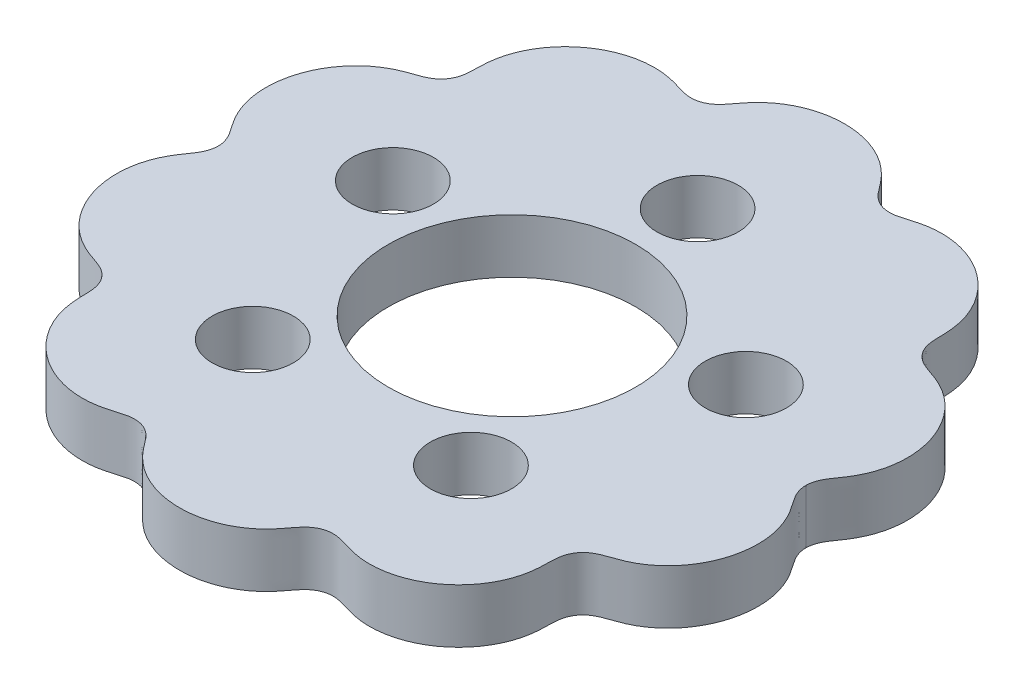
SolidWorks part; units mm, degrees
material "PET"
ref_plane "Front Plane" through (0, 0, 0) normal (0, 0, 1) x (1, 0, 0)
ref_plane "Top Plane" through (0, 0, 0) normal (0, 1, 0) x (1, 0, 0)
ref_plane "Right Plane" through (0, 0, 0) normal (1, 0, 0) x (0, 0, -1)
sketch "Sketch3" plane through (0, 0, 0) normal (0, 1, 0) x (1, 0, 0)
  line L0 (-38, 0) -> (38, 0) construction
  spline S0 degree 4 poles (36.1126, 19.4729) (36.4413, 19.2702) (37.0789, 18.8327) (37.9693, 18.0854) (38.8762, 17.0775) (39.5507, 16.1331) (40.0407, 15.3004) (40.3881, 14.6099) (40.6897, 13.8983) (40.9444, 13.1686) (41.1512, 12.4238) (41.3092, 11.6672) (41.4173, 10.9019) (41.4749, 10.1311) (41.4811, 9.3582) (41.4409, 8.6831) (41.3791, 8.1554) (41.3187, 7.774) (41.2754, 7.5365) (41.2375, 7.3472) (41.1962, 7.1586) (41.1515, 6.9704) (41.1034, 6.7831) (41.0529, 6.5992) (41.0057, 6.4387) (40.9596, 6.292) (40.911, 6.1433) (40.8605, 5.994) (40.8241, 5.8921) (40.7629, 5.7282) (40.696, 5.5563) (40.6301, 5.3943) (40.5534, 5.2164) (40.4594, 5.0098) (40.3608, 4.8047) (40.2582, 4.6024) (40.1246, 4.3522) (39.9561, 4.0563) (39.7484, 3.7177) (39.4981, 3.339) (39.2376, 2.965) (38.9734, 2.5913) (38.7158, 2.2107) (38.4789, 1.8141) (38.1957, 1.2291) (37.9766, 0.4652) (37.9635, -0.3716) (38.1843, -1.2042) (38.4978, -1.8638) (38.846, -2.4146) (39.2404, -2.9665) (39.6428, -3.5471) (40.0239, -4.1584) (40.3719, -4.8049) (40.7581, -5.6601) (41.2492, -7.104) (41.5283, -8.8063) (41.497, -10.7209) (41.0681, -12.9695) (40.261, -15.1202) (39.0103, -17.0606) (37.5039, -18.5357) (36.2533, -19.4084) (35.4358, -19.8689) (34.7726, -20.1839) (34.1039, -20.4514) (33.4364, -20.6827) (32.7933, -20.8983) (32.1897, -21.1442) (31.5529, -21.5019) (30.9312, -22.0245) (30.4594, -22.6931) (30.1741, -23.4534) (30.0458, -24.1722) (30.007, -24.8226) (30.0023, -25.501) (29.9851, -26.2073) (29.932, -26.9257) (29.8311, -27.653) (29.6377, -28.5713) (29.2954, -29.6627) (28.7481, -30.8814) (27.737, -32.4998) (26.4511, -33.9241) (24.9383, -35.11) (22.9085, -36.2017) (21.0718, -36.809) (19.3456, -37.0491) (17.8057, -37.0035) (16.875, -36.8848) (16.1662, -36.7445) (15.49, -36.5679) (14.8442, -36.3701) (14.2164, -36.1743) (13.5933, -36.023) (12.8676, -35.9405) (12.0528, -36.0041) (11.2809, -36.2742) (10.6112, -36.7228) (10.0954, -37.2217) (9.6902, -37.7143) (9.2961, -38.2479) (8.8778, -38.7968) (8.4239, -39.3374) (7.9264, -39.8602) (7.2439, -40.4854) (6.0405, -41.3936) (4.1944, -42.3611) (1.6143, -43.0524) (-1.0601, -43.0726) (-3.3015, -42.6065) (-5.0731, -41.8972) (-6.2345, -41.2367) (-7.1553, -40.5581) (-7.8537, -39.9313) (-8.3647, -39.4039) (-8.8316, -38.8552) (-9.2618, -38.2946) (-9.6641, -37.7484) (-10.0754, -37.2431) (-10.5976, -36.7328) (-11.2728, -36.2773) (-12.0499, -36.0044) (-12.8676, -35.9405) (-13.5933, -36.023) (-14.2164, -36.1743) (-14.8442, -36.3701) (-15.49, -36.5679) (-16.1662, -36.7445) (-16.875, -36.8848) (-17.8057, -37.0035) (-19.3456, -37.0491) (-21.0718, -36.809) (-22.9085, -36.2017) (-24.9383, -35.11) (-26.4511, -33.9241) (-27.737, -32.4998) (-28.7481, -30.8814) (-29.2954, -29.6627) (-29.6377, -28.5713) (-29.8311, -27.653) (-29.932, -26.9257) (-29.9851, -26.2073) (-30.0023, -25.501) (-30.007, -24.8226) (-30.0458, -24.1722) (-30.1741, -23.4534) (-30.4594, -22.6931) (-30.9312, -22.0245) (-31.5529, -21.5019) (-32.1897, -21.1442) (-32.7933, -20.8983) (-33.4364, -20.6827) (-34.1039, -20.4514) (-34.7726, -20.1839) (-35.4358, -19.8689) (-36.2533, -19.4084) (-37.5039, -18.5357) (-39.0102, -17.0606) (-40.4695, -14.7968) (-41.4272, -11.8731) (-41.5902, -9.1846) (-41.2492, -7.104) (-40.758, -5.6601) (-40.3719, -4.8049) (-40.0239, -4.1584) (-39.6428, -3.5471) (-39.2404, -2.9665) (-38.8459, -2.4146) (-38.4978, -1.8639) (-38.1843, -1.2042) (-37.9635, -0.3717) (-37.9784, 0.5829) (-38.2703, 1.4507) (-38.6513, 2.1149) (-38.9734, 2.5914) (-39.2377, 2.965) (-39.4981, 3.339) (-39.7485, 3.7177) (-39.9561, 4.0563) (-40.1246, 4.3522) (-40.2582, 4.6024) (-40.3608, 4.8047) (-40.4594, 5.0098) (-40.5534, 5.2164) (-40.6301, 5.3943) (-40.696, 5.5563) (-40.7629, 5.7282) (-40.8242, 5.8922) (-40.866, 6.0095) (-40.9533, 6.269) (-41.0431, 6.5583) (-41.1159, 6.8262) (-41.1862, 7.1122) (-41.2375, 7.3472) (-41.2754, 7.5365) (-41.3187, 7.774) (-41.3791, 8.1554) (-41.4409, 8.6831) (-41.4811, 9.3582) (-41.4749, 10.1311) (-41.4173, 10.9019) (-41.3092, 11.6672) (-41.1512, 12.4238) (-40.9444, 13.1686) (-40.6897, 13.8983) (-40.3881, 14.6099) (-40.0407, 15.3004) (-39.5507, 16.1331) (-38.8762, 17.0776) (-37.9693, 18.0854) (-37.0789, 18.8327) (-36.4413, 19.2702) (-36.1126, 19.4729) knots 0 0 0 0 0 0.008318 0.016636 0.024955 0.029115 0.033274 0.037433 0.041593 0.045752 0.049911 0.054071 0.05823 0.062389 0.066549 0.070708 0.072787 0.073827 0.074867 0.075907 0.076947 0.077986 0.079026 0.080066 0.081106 0.081626 0.082146 0.083185 0.084407 0.085018 0.085629 0.086851 0.088074 0.089296 0.090518 0.09174 0.092962 0.095406 0.09785 0.100294 0.102738 0.105223 0.107708 0.110193 0.112678 0.119205 0.124677 0.127881 0.131086 0.134889 0.138693 0.142496 0.1463 0.150398 0.154496 0.162692 0.179083 0.187278 0.195474 0.211865 0.228255 0.23645 0.240548 0.244645 0.248449 0.252252 0.256055 0.259858 0.263063 0.266267 0.271739 0.277211 0.280415 0.283619 0.287423 0.291227 0.295031 0.298835 0.302933 0.307031 0.315227 0.323423 0.331619 0.348011 0.35629 0.364568 0.381124 0.389403 0.393542 0.397682 0.401318 0.404955 0.408591 0.412227 0.415486 0.418745 0.424273 0.429682 0.432828 0.435974 0.439689 0.443405 0.44712 0.450835 0.454887 0.458938 0.467041 0.483246 0.499452 0.515845 0.524041 0.532238 0.540434 0.544532 0.548631 0.552435 0.556239 0.560043 0.563848 0.567052 0.570256 0.575727 0.581255 0.584514 0.587773 0.591409 0.595045 0.598682 0.602318 0.606458 0.610597 0.618876 0.635432 0.64371 0.651989 0.668381 0.676577 0.684773 0.692969 0.697067 0.701165 0.704969 0.708773 0.712577 0.716381 0.719585 0.722789 0.728261 0.733733 0.736937 0.740142 0.743945 0.747748 0.751551 0.755355 0.759452 0.76355 0.771745 0.788135 0.804526 0.820917 0.837308 0.845504 0.849602 0.8537 0.857504 0.861307 0.865111 0.868914 0.872119 0.875323 0.880795 0.887322 0.892292 0.894777 0.897262 0.899706 0.90215 0.904594 0.907038 0.90826 0.909482 0.910704 0.911926 0.913149 0.914371 0.914982 0.915593 0.916815 0.917854 0.918894 0.920974 0.923053 0.924093 0.925133 0.926173 0.927213 0.929292 0.933451 0.937611 0.94177 0.945929 0.950089 0.954248 0.958407 0.962567 0.966726 0.970885 0.975045 0.983364 0.991682 1 1 1 1 1 construction
  spline S1 degree 4 poles (38, 0) (38, -0.0025) (38.0002, -0.2591) (38.0411, -0.6644) (38.1843, -1.2042) (38.4978, -1.8638) (38.846, -2.4146) (39.2404, -2.9665) (39.6428, -3.5471) (40.0239, -4.1584) (40.3719, -4.8049) (40.7581, -5.6601) (41.2492, -7.104) (41.5283, -8.8063) (41.497, -10.7209) (41.0681, -12.9695) (40.261, -15.1202) (39.0103, -17.0606) (37.5039, -18.5357) (36.2533, -19.4084) (35.4358, -19.8689) (34.7726, -20.1839) (34.1039, -20.4514) (33.4364, -20.6827) (32.7933, -20.8983) (32.1897, -21.1442) (31.5529, -21.5019) (30.9312, -22.0245) (30.4594, -22.6931) (30.1741, -23.4534) (30.0458, -24.1722) (30.007, -24.8226) (30.0023, -25.501) (29.9851, -26.2073) (29.932, -26.9257) (29.8311, -27.653) (29.6377, -28.5713) (29.2954, -29.6627) (28.7481, -30.8814) (27.737, -32.4998) (26.4511, -33.9241) (24.9383, -35.11) (22.9085, -36.2017) (21.0718, -36.809) (19.3456, -37.0491) (17.8057, -37.0035) (16.875, -36.8848) (16.1662, -36.7445) (15.49, -36.5679) (14.8442, -36.3701) (14.2164, -36.1743) (13.5933, -36.023) (12.8676, -35.9405) (12.0528, -36.0041) (11.2809, -36.2742) (10.6112, -36.7228) (10.0954, -37.2217) (9.6902, -37.7143) (9.2961, -38.2479) (8.8778, -38.7968) (8.4239, -39.3374) (7.9264, -39.8602) (7.2439, -40.4854) (6.0405, -41.3936) (4.1944, -42.3611) (1.6143, -43.0524) (-1.0601, -43.0726) (-3.3015, -42.6065) (-5.0731, -41.8972) (-6.2345, -41.2367) (-7.1553, -40.5581) (-7.8537, -39.9313) (-8.3647, -39.4039) (-8.8316, -38.8552) (-9.2618, -38.2946) (-9.6641, -37.7484) (-10.0754, -37.2431) (-10.5976, -36.7328) (-11.2728, -36.2773) (-12.0499, -36.0044) (-12.8676, -35.9405) (-13.5933, -36.023) (-14.2164, -36.1743) (-14.8442, -36.3701) (-15.49, -36.5679) (-16.1662, -36.7445) (-16.875, -36.8848) (-17.8057, -37.0035) (-19.3456, -37.0491) (-21.0718, -36.809) (-22.9085, -36.2017) (-24.9383, -35.11) (-26.4511, -33.9241) (-27.737, -32.4998) (-28.7481, -30.8814) (-29.2954, -29.6627) (-29.6377, -28.5713) (-29.8311, -27.653) (-29.932, -26.9257) (-29.9851, -26.2073) (-30.0023, -25.501) (-30.007, -24.8226) (-30.0458, -24.1722) (-30.1741, -23.4534) (-30.4594, -22.6931) (-30.9312, -22.0245) (-31.5529, -21.5019) (-32.1897, -21.1442) (-32.7933, -20.8983) (-33.4364, -20.6827) (-34.1039, -20.4514) (-34.7726, -20.1839) (-35.4358, -19.8689) (-36.2533, -19.4084) (-37.5039, -18.5357) (-39.0102, -17.0606) (-40.4695, -14.7968) (-41.4272, -11.8731) (-41.5902, -9.1846) (-41.2492, -7.104) (-40.758, -5.6601) (-40.3719, -4.8049) (-40.0239, -4.1584) (-39.6428, -3.5471) (-39.2404, -2.9665) (-38.8459, -2.4146) (-38.4978, -1.8639) (-38.1843, -1.2042) (-38.0411, -0.6644) (-38.0002, -0.2591) (-38, -0.0025) (-38, 0) knots 0.119151 0.119151 0.119151 0.119151 0.119151 0.119205 0.124677 0.127881 0.131086 0.134889 0.138693 0.142496 0.1463 0.150398 0.154496 0.162692 0.179083 0.187278 0.195474 0.211865 0.228255 0.23645 0.240548 0.244645 0.248449 0.252252 0.256055 0.259858 0.263063 0.266267 0.271739 0.277211 0.280415 0.283619 0.287423 0.291227 0.295031 0.298835 0.302933 0.307031 0.315227 0.323423 0.331619 0.348011 0.35629 0.364568 0.381124 0.389403 0.393542 0.397682 0.401318 0.404955 0.408591 0.412227 0.415486 0.418745 0.424273 0.429682 0.432828 0.435974 0.439689 0.443405 0.44712 0.450835 0.454887 0.458938 0.467041 0.483246 0.499452 0.515845 0.524041 0.532238 0.540434 0.544532 0.548631 0.552435 0.556239 0.560043 0.563848 0.567052 0.570256 0.575727 0.581255 0.584514 0.587773 0.591409 0.595045 0.598682 0.602318 0.606458 0.610597 0.618876 0.635432 0.64371 0.651989 0.668381 0.676577 0.684773 0.692969 0.697067 0.701165 0.704969 0.708773 0.712577 0.716381 0.719585 0.722789 0.728261 0.733733 0.736937 0.740142 0.743945 0.747748 0.751551 0.755355 0.759452 0.76355 0.771745 0.788135 0.804526 0.820917 0.837308 0.845504 0.849602 0.8537 0.857504 0.861307 0.865111 0.868914 0.872119 0.875323 0.880795 0.880849 0.880849 0.880849 0.880849 0.880849
  spline S2 degree 4 poles (38, 0) (38, 0.0025) (38.0002, 0.2591) (38.0411, 0.6644) (38.1843, 1.2042) (38.4978, 1.8638) (38.846, 2.4146) (39.2404, 2.9665) (39.6428, 3.5471) (40.0239, 4.1584) (40.3719, 4.8049) (40.7581, 5.6601) (41.2492, 7.104) (41.5283, 8.8063) (41.497, 10.7209) (41.0681, 12.9695) (40.261, 15.1202) (39.0103, 17.0606) (37.5039, 18.5357) (36.2533, 19.4084) (35.4358, 19.8689) (34.7726, 20.1839) (34.1039, 20.4514) (33.4364, 20.6827) (32.7933, 20.8983) (32.1897, 21.1442) (31.5529, 21.5019) (30.9312, 22.0245) (30.4594, 22.6931) (30.1741, 23.4534) (30.0458, 24.1722) (30.007, 24.8226) (30.0023, 25.501) (29.9851, 26.2073) (29.932, 26.9257) (29.8311, 27.653) (29.6377, 28.5713) (29.2954, 29.6627) (28.7481, 30.8814) (27.737, 32.4998) (26.4511, 33.9241) (24.9383, 35.11) (22.9085, 36.2017) (21.0718, 36.809) (19.3456, 37.0491) (17.8057, 37.0035) (16.875, 36.8848) (16.1662, 36.7445) (15.49, 36.5679) (14.8442, 36.3701) (14.2164, 36.1743) (13.5933, 36.023) (12.8676, 35.9405) (12.0528, 36.0041) (11.2809, 36.2742) (10.6112, 36.7228) (10.0954, 37.2217) (9.6902, 37.7143) (9.2961, 38.2479) (8.8778, 38.7968) (8.4239, 39.3374) (7.9264, 39.8602) (7.2439, 40.4854) (6.0405, 41.3936) (4.1944, 42.3611) (1.6143, 43.0524) (-1.0601, 43.0726) (-3.3015, 42.6065) (-5.0731, 41.8972) (-6.2345, 41.2367) (-7.1553, 40.5581) (-7.8537, 39.9313) (-8.3647, 39.4039) (-8.8316, 38.8552) (-9.2618, 38.2946) (-9.6641, 37.7484) (-10.0754, 37.2431) (-10.5976, 36.7328) (-11.2728, 36.2773) (-12.0499, 36.0044) (-12.8676, 35.9405) (-13.5933, 36.023) (-14.2164, 36.1743) (-14.8442, 36.3701) (-15.49, 36.5679) (-16.1662, 36.7445) (-16.875, 36.8848) (-17.8057, 37.0035) (-19.3456, 37.0491) (-21.0718, 36.809) (-22.9085, 36.2017) (-24.9383, 35.11) (-26.4511, 33.9241) (-27.737, 32.4998) (-28.7481, 30.8814) (-29.2954, 29.6627) (-29.6377, 28.5713) (-29.8311, 27.653) (-29.932, 26.9257) (-29.9851, 26.2073) (-30.0023, 25.501) (-30.007, 24.8226) (-30.0458, 24.1722) (-30.1741, 23.4534) (-30.4594, 22.6931) (-30.9312, 22.0245) (-31.5529, 21.5019) (-32.1897, 21.1442) (-32.7933, 20.8983) (-33.4364, 20.6827) (-34.1039, 20.4514) (-34.7726, 20.1839) (-35.4358, 19.8689) (-36.2533, 19.4084) (-37.5039, 18.5357) (-39.0102, 17.0606) (-40.4695, 14.7968) (-41.4272, 11.8731) (-41.5902, 9.1846) (-41.2492, 7.104) (-40.758, 5.6601) (-40.3719, 4.8049) (-40.0239, 4.1584) (-39.6428, 3.5471) (-39.2404, 2.9665) (-38.8459, 2.4146) (-38.4978, 1.8639) (-38.1843, 1.2042) (-38.0411, 0.6644) (-38.0002, 0.2591) (-38, 0.0025) (-38, 0) knots 0.119151 0.119151 0.119151 0.119151 0.119151 0.119205 0.124677 0.127881 0.131086 0.134889 0.138693 0.142496 0.1463 0.150398 0.154496 0.162692 0.179083 0.187278 0.195474 0.211865 0.228255 0.23645 0.240548 0.244645 0.248449 0.252252 0.256055 0.259858 0.263063 0.266267 0.271739 0.277211 0.280415 0.283619 0.287423 0.291227 0.295031 0.298835 0.302933 0.307031 0.315227 0.323423 0.331619 0.348011 0.35629 0.364568 0.381124 0.389403 0.393542 0.397682 0.401318 0.404955 0.408591 0.412227 0.415486 0.418745 0.424273 0.429682 0.432828 0.435974 0.439689 0.443405 0.44712 0.450835 0.454887 0.458938 0.467041 0.483246 0.499452 0.515845 0.524041 0.532238 0.540434 0.544532 0.548631 0.552435 0.556239 0.560043 0.563848 0.567052 0.570256 0.575727 0.581255 0.584514 0.587773 0.591409 0.595045 0.598682 0.602318 0.606458 0.610597 0.618876 0.635432 0.64371 0.651989 0.668381 0.676577 0.684773 0.692969 0.697067 0.701165 0.704969 0.708773 0.712577 0.716381 0.719585 0.722789 0.728261 0.733733 0.736937 0.740142 0.743945 0.747748 0.751551 0.755355 0.759452 0.76355 0.771745 0.788135 0.804526 0.820917 0.837308 0.845504 0.849602 0.8537 0.857504 0.861307 0.865111 0.868914 0.872119 0.875323 0.880795 0.880849 0.880849 0.880849 0.880849 0.880849
extrude "Boss-Extrude2" add sketch "Sketch3" along normal blind 7
sketch "Sketch4" plane through (0, 7, 0) normal (0, 1, 0) x (1, 0, 0)
  line L0 (0, 0) -> (40.8955, 13.2876) construction
  circle A0 centre (0, 0) radius 16
  circle A1 centre (22.8254, 7.4164) radius 5.25
  circle A2 centre (14.1068, -19.4164) radius 5.25
  circle A3 centre (-14.1069, -19.4164) radius 5.25
  circle A4 centre (-22.8253, 7.4165) radius 5.25
  circle A5 centre (0.0001, 24) radius 5.25
  spline S0 degree 4 poles (38, 0) (38, 0.0025) (38.0002, 0.2591) (38.0411, 0.6644) (38.1843, 1.2042) (38.4978, 1.8638) (38.846, 2.4146) (39.2404, 2.9665) (39.6428, 3.5471) (40.0239, 4.1584) (40.3719, 4.8049) (40.7581, 5.6601) (41.2492, 7.104) (41.5283, 8.8063) (41.497, 10.7209) (41.0681, 12.9695) (40.261, 15.1202) (39.0103, 17.0606) (37.5039, 18.5357) (36.2533, 19.4084) (35.4358, 19.8689) (34.7726, 20.1839) (34.1039, 20.4514) (33.4364, 20.6827) (32.7933, 20.8983) (32.1897, 21.1442) (31.5529, 21.5019) (30.9312, 22.0245) (30.4594, 22.6931) (30.1741, 23.4534) (30.0458, 24.1722) (30.007, 24.8226) (30.0023, 25.501) (29.9851, 26.2073) (29.932, 26.9257) (29.8311, 27.653) (29.6377, 28.5713) (29.2954, 29.6627) (28.7481, 30.8814) (27.737, 32.4998) (26.4511, 33.9241) (24.9383, 35.11) (22.9085, 36.2017) (21.0718, 36.809) (19.3456, 37.0491) (17.8057, 37.0035) (16.875, 36.8848) (16.1662, 36.7445) (15.49, 36.5679) (14.8442, 36.3701) (14.2164, 36.1743) (13.5933, 36.023) (12.8676, 35.9405) (12.0528, 36.0041) (11.2809, 36.2742) (10.6112, 36.7228) (10.0954, 37.2217) (9.6902, 37.7143) (9.2961, 38.2479) (8.8778, 38.7968) (8.4239, 39.3374) (7.9264, 39.8602) (7.2439, 40.4854) (6.0405, 41.3936) (4.1944, 42.3611) (1.6143, 43.0524) (-1.0601, 43.0726) (-3.3015, 42.6065) (-5.0731, 41.8972) (-6.2345, 41.2367) (-7.1553, 40.5581) (-7.8537, 39.9313) (-8.3647, 39.4039) (-8.8316, 38.8552) (-9.2618, 38.2946) (-9.6641, 37.7484) (-10.0754, 37.2431) (-10.5976, 36.7328) (-11.2728, 36.2773) (-12.0499, 36.0044) (-12.8676, 35.9405) (-13.5933, 36.023) (-14.2164, 36.1743) (-14.8442, 36.3701) (-15.49, 36.5679) (-16.1662, 36.7445) (-16.875, 36.8848) (-17.8057, 37.0035) (-19.3456, 37.0491) (-21.0718, 36.809) (-22.9085, 36.2017) (-24.9383, 35.11) (-26.4511, 33.9241) (-27.737, 32.4998) (-28.7481, 30.8814) (-29.2954, 29.6627) (-29.6377, 28.5713) (-29.8311, 27.653) (-29.932, 26.9257) (-29.9851, 26.2073) (-30.0023, 25.501) (-30.007, 24.8226) (-30.0458, 24.1722) (-30.1741, 23.4534) (-30.4594, 22.6931) (-30.9312, 22.0245) (-31.5529, 21.5019) (-32.1897, 21.1442) (-32.7933, 20.8983) (-33.4364, 20.6827) (-34.1039, 20.4514) (-34.7726, 20.1839) (-35.4358, 19.8689) (-36.2533, 19.4084) (-37.5039, 18.5357) (-39.0102, 17.0606) (-40.4695, 14.7968) (-41.4272, 11.8731) (-41.5902, 9.1846) (-41.2492, 7.104) (-40.758, 5.6601) (-40.3719, 4.8049) (-40.0239, 4.1584) (-39.6428, 3.5471) (-39.2404, 2.9665) (-38.8459, 2.4146) (-38.4978, 1.8639) (-38.1843, 1.2042) (-38.0411, 0.6644) (-38.0002, 0.2591) (-38, 0.0025) (-38, 0) knots 0.119151 0.119151 0.119151 0.119151 0.119151 0.119205 0.124677 0.127881 0.131086 0.134889 0.138693 0.142496 0.1463 0.150398 0.154496 0.162692 0.179083 0.187278 0.195474 0.211865 0.228255 0.23645 0.240548 0.244645 0.248449 0.252252 0.256055 0.259858 0.263063 0.266267 0.271739 0.277211 0.280415 0.283619 0.287423 0.291227 0.295031 0.298835 0.302933 0.307031 0.315227 0.323423 0.331619 0.348011 0.35629 0.364568 0.381124 0.389403 0.393542 0.397682 0.401318 0.404955 0.408591 0.412227 0.415486 0.418745 0.424273 0.429682 0.432828 0.435974 0.439689 0.443405 0.44712 0.450835 0.454887 0.458938 0.467041 0.483246 0.499452 0.515845 0.524041 0.532238 0.540434 0.544532 0.548631 0.552435 0.556239 0.560043 0.563848 0.567052 0.570256 0.575727 0.581255 0.584514 0.587773 0.591409 0.595045 0.598682 0.602318 0.606458 0.610597 0.618876 0.635432 0.64371 0.651989 0.668381 0.676577 0.684773 0.692969 0.697067 0.701165 0.704969 0.708773 0.712577 0.716381 0.719585 0.722789 0.728261 0.733733 0.736937 0.740142 0.743945 0.747748 0.751551 0.755355 0.759452 0.76355 0.771745 0.788135 0.804526 0.820917 0.837308 0.845504 0.849602 0.8537 0.857504 0.861307 0.865111 0.868914 0.872119 0.875323 0.880795 0.880849 0.880849 0.880849 0.880849 0.880849 construction
  point P19 (0, 0)
  dimension "D1" = 32
  dimension "D2" = 10.5
  dimension "D3" = 24
  dimension "D4" = 5
extrude "Cut-Extrude2" cut sketch "Sketch4" against normal blind 7
